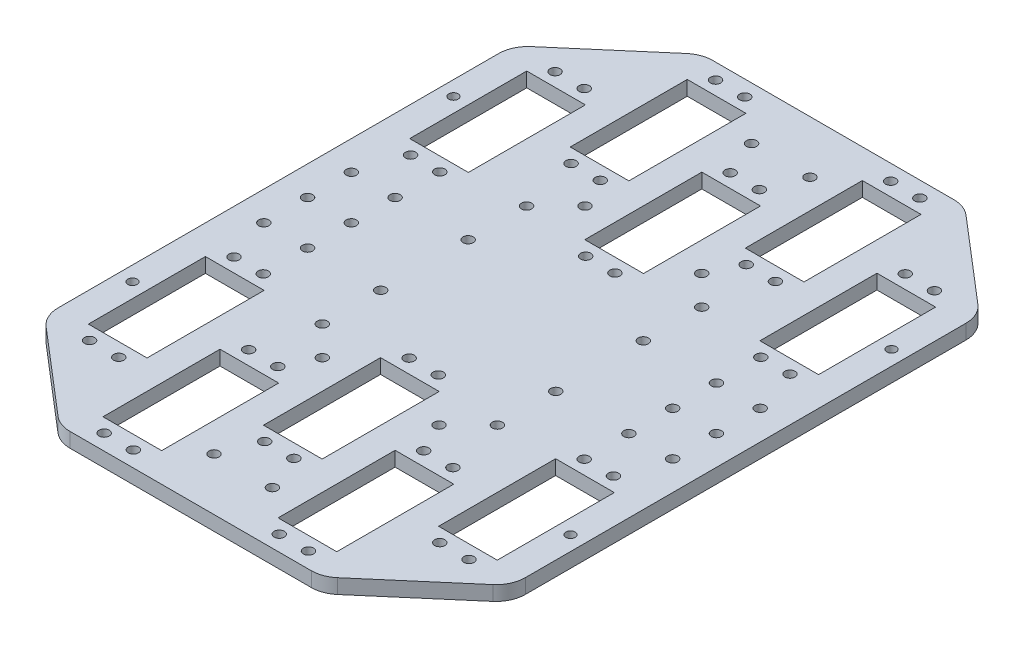
SolidWorks part; units mm, degrees
ref_plane "正面(Front)" through (0, 0, 0) normal (0, 0, 1) x (1, 0, 0)
ref_plane "平面(Top)" through (0, 0, 0) normal (0, 1, 0) x (1, 0, 0)
ref_plane "右側面(Right)" through (0, 0, 0) normal (1, 0, 0) x (0, 0, -1)
sketch "ｽｹｯﾁ1" plane through (0, 0, 0) normal (0, 1, 0) x (1, 0, 0)
  line L0 (0, 0) -> (0, 109.1944) construction
  line L1 (-80.05, 0) -> (80.05, 0)
  line L2 (80.05, 0) -> (80.05, 85.1)
  line L3 (80.05, 85.1) -> (-80.05, 85.1)
  line L4 (-10.05, 20) -> (10.05, 20) construction
  line L5 (-10.05, 50.1) -> (10.05, 50.1)
  line L6 (-10.05, 50.1) -> (-10.05, 10)
  line L7 (-10.05, 10) -> (10.05, 10)
  line L8 (10.05, 50.1) -> (10.05, 10)
  line L9 (-10.05, 50.1) -> (10.05, 10) construction
  line L10 (-10.05, 10) -> (10.05, 50.1) construction
  line L11 (49.95, 50.1) -> (70.05, 50.1)
  line L12 (49.95, 50.1) -> (49.95, 10)
  line L13 (49.95, 10) -> (70.05, 10)
  line L14 (70.05, 50.1) -> (70.05, 10)
  line L15 (49.95, 50.1) -> (70.05, 10) construction
  line L16 (49.95, 10) -> (70.05, 50.1) construction
  line L17 (19.95, 75.1) -> (40.05, 75.1)
  line L18 (19.95, 75.1) -> (19.95, 35)
  line L19 (19.95, 35) -> (40.05, 35)
  line L20 (40.05, 75.1) -> (40.05, 35)
  line L21 (19.95, 75.1) -> (40.05, 35) construction
  line L22 (19.95, 35) -> (40.05, 75.1) construction
  line L23 (19.95, 65.1) -> (40.05, 65.1) construction
  line L24 (-80.05, 0) -> (-80.05, 85.1)
  line L25 (-49.95, 10) -> (-70.05, 10)
  line L26 (-70.05, 50.1) -> (-70.05, 10)
  line L27 (-49.95, 50.1) -> (-70.05, 50.1)
  line L28 (-49.95, 50.1) -> (-49.95, 10)
  line L29 (-19.95, 35) -> (-40.05, 35)
  line L30 (-40.05, 75.1) -> (-40.05, 35)
  line L31 (-19.95, 75.1) -> (-40.05, 75.1)
  line L32 (-19.95, 75.1) -> (-19.95, 35)
  point P3 (60, 30.05)
  point P7 (0, 30.05)
  point P17 (30, 55.05)
  point P26 (0, 85.1)
  dimension "D1" = 10
  dimension "D2" = 10
  dimension "D3" = 40.1
  dimension "D4" = 20.1
  dimension "D5" = 10
  dimension "D6" = 60
  dimension "D7" = 10
  dimension "D8" = 35
  dimension "D9" = 30
  dimension "D10" = 10
  dimension "D11" = 54.1665
extrude "ﾎﾞｽ - 押し出し1" add sketch "ｽｹｯﾁ1" along normal blind 5
sketch "ｽｹｯﾁ2" plane through (0, 5, 0) normal (0, 1, 0) x (1, 0, 0)
  line L0 (0, 0) -> (0, 107.4363) construction
  line L1 (80.05, 55.1) -> (45.05, 85.1)
  line L2 (80.05, 0) -> (80.05, 85.1) construction
  line L3 (80.05, 85.1) -> (-80.05, 85.1) construction
  line L4 (70.05, 50.1) -> (49.95, 50.1) construction
  line L7 (40.05, 35) -> (40.05, 75.1) construction
  line L8 (-80.05, 55.1) -> (-45.05, 85.1)
  line L9 (-45.05, 85.1) -> (45.05, 85.1)
  dimension "D1" = 5
  dimension "D2" = 5
extrude "ｶｯﾄ - 押し出し1" cut sketch "ｽｹｯﾁ2" against normal through all and the other way through all
sketch "ｽｹｯﾁ3" plane through (0, 5, 0) normal (0, 1, 0) x (1, 0, 0)
  line L1 (80.05, 5.25) -> (-114.5257, 5.25) construction
  line L2 (80.05, 0) -> (80.05, 55.1) construction
  line L3 (49.95, 10) -> (70.05, 10) construction
  line L4 (60, 10) -> (60, -5.8436) construction
  line L5 (0, 10) -> (0, -14.4968) construction
  line L6 (-10.05, 10) -> (10.05, 10) construction
  line L7 (-60, 10) -> (-60, -11.451) construction
  line L8 (-70.05, 10) -> (-49.95, 10) construction
  line L9 (-51.2917, 79.75) -> (55, 79.75) construction
  line L10 (-45.05, 85.1) -> (-80.05, 55.1) construction
  line L12 (-19.95, 75.1) -> (-40.05, 75.1) construction
  line L13 (-30, 75.1) -> (-30, 103.3573) construction
  line L14 (30, 75.1) -> (30, 100.8275) construction
  line L15 (40.05, 75.1) -> (19.95, 75.1) construction
  line L16 (81.9855, 54.75) -> (-83.6019, 54.75) construction
  line L17 (70.05, 50.1) -> (49.95, 50.1) construction
  line L18 (60, 50.1) -> (60, 65.5905) construction
  line L19 (0, 50.1) -> (0, 65.5905) construction
  line L20 (10.05, 50.1) -> (-10.05, 50.1) construction
  line L21 (-60, 50.1) -> (-60, 65.5905) construction
  line L22 (-49.95, 50.1) -> (-70.05, 50.1) construction
  line L23 (-55, 30.25) -> (61.2022, 30.25) construction
  line L24 (-40.05, 35) -> (-19.95, 35) construction
  line L25 (-30, 35) -> (-30, 33.4215) construction
  line L26 (30, 35) -> (30, 28.9495) construction
  line L27 (19.95, 35) -> (40.05, 35) construction
  circle A0 centre (65, 5.25) radius 1.75
  circle A1 centre (55, 5.25) radius 1.75
  circle A2 centre (5, 5.25) radius 1.75
  circle A3 centre (-5, 5.25) radius 1.75
  circle A4 centre (-55, 5.25) radius 1.75
  circle A5 centre (-65, 5.25) radius 1.75
  circle A6 centre (-35, 79.75) radius 1.75
  circle A7 centre (-25, 79.75) radius 1.75
  circle A8 centre (25, 79.75) radius 1.75
  circle A9 centre (35, 79.75) radius 1.75
  circle A10 centre (65, 54.75) radius 1.75
  circle A11 centre (55, 54.75) radius 1.75
  circle A12 centre (5, 54.75) radius 1.75
  circle A13 centre (-5, 54.75) radius 1.75
  circle A14 centre (-55, 54.75) radius 1.75
  circle A15 centre (-65, 54.75) radius 1.75
  circle A16 centre (-35, 30.25) radius 1.75
  circle A17 centre (-25, 30.25) radius 1.75
  circle A18 centre (25, 30.25) radius 1.75
  circle A19 centre (35, 30.25) radius 1.75
  dimension "D1" = 4.75
  dimension "D2" = 10
  dimension "D3" = 3.5
  dimension "D4" = 10
  dimension "D5" = 10
  dimension "D7" = 10
  dimension "D8" = 10
  dimension "D10" = 10
  dimension "D11" = 10
  dimension "D12" = 10
  dimension "D14" = 10
  dimension "D15" = 10
  dimension "D6" = 4.65
  dimension "D9" = 4.65
  dimension "D13" = 4.75
extrude "ｶｯﾄ - 押し出し2" cut sketch "ｽｹｯﾁ3" against normal through all
sketch "ｽｹｯﾁ4" plane through (0, 5, 0) normal (0, 1, 0) x (1, 0, 0)
  line L0 (0, 0) -> (0, 98.9038) construction
  line L1 (-80.05, 0) -> (80.05, 0) construction
  circle A0 centre (30, 10) radius 1.75
  circle A1 centre (-30, 10) radius 1.75
  circle A2 centre (20, 20) radius 1.75
  circle A3 centre (-20, 20) radius 1.75
  dimension "D1" = 10
  dimension "D2" = 60
  dimension "D3" = 3.5
  dimension "D4" = 10
  dimension "D5" = 10
extrude "ｶｯﾄ - 押し出し3" cut sketch "ｽｹｯﾁ4" against normal through all
ref_plane "平面1" through (0, 0, 25) normal (0, 0, 1) x (1, 0, 0)
sketch "ｽｹｯﾁ5" plane through (0, 5, 0) normal (0, 1, 0) x (1, 0, 0)
  line L0 (0, 0) -> (0, 107.3691) construction
  line L1 (45.05, 85.1) -> (-45.05, 85.1) construction
  circle A0 centre (-10, 67.1) radius 1.75
  circle A1 centre (10, 67.1) radius 1.75
  dimension "D1" = 3.5
  dimension "D2" = 20
  dimension "D3" = 18
extrude "ｶｯﾄ - 押し出し4" cut sketch "ｽｹｯﾁ5" against normal through all
mirror "ﾐﾗｰ2" about plane through (0, 0, 25) normal (0, 0, 1) of bodies 107 105
sketch "ｽｹｯﾁ6" plane through (0, 5, 0) normal (0, 1, 0) x (1, 0, 0)
  line L0 (-80.05, 0) -> (-80.05, -50)
  line L1 (-80.05, -50) -> (80.05, -50)
  line L2 (80.05, -50) -> (80.05, 0)
  line L3 (80.05, 0) -> (-80.05, 0)
extrude "ﾎﾞｽ - 押し出し2" add sketch "ｽｹｯﾁ6" against normal up to surface (5 mm away) up to face at (-10, 0, -65.35)
sketch "ｽｹｯﾁ7" plane through (0, 5, 0) normal (0, 1, 0) x (1, 0, 0)
  line L0 (-80.05, -25) -> (80.05, -25) construction
  line L1 (-80.05, -105.1) -> (-80.05, 55.1) construction
  line L2 (80.05, 55.1) -> (80.05, -105.1) construction
  line L4 (-30, -10) -> (30, -10) construction
  line L5 (-30, -10) -> (-30, -40) construction
  line L6 (-30, -40) -> (30, -40) construction
  line L7 (30, -10) -> (30, -40) construction
  line L8 (-30, -10) -> (30, -40) construction
  line L9 (-30, -40) -> (30, -10) construction
  circle A0 centre (-30, -10) radius 1.75
  circle A1 centre (-30, -40) radius 1.75
  circle A2 centre (30, -40) radius 1.75
  circle A3 centre (30, -10) radius 1.75
  point P6 (0, -25)
  dimension "D3" = 3.5
  dimension "D1" = 30
  dimension "D2" = 60
extrude "ｶｯﾄ - 押し出し5" cut sketch "ｽｹｯﾁ7" against normal through all
sketch "ｽｹｯﾁ8" plane through (0, 5, 0) normal (0, 1, 0) x (1, 0, 0)
  line L0 (-80.05, -25) -> (80.05, -25) construction
  line L1 (-80.05, -105.1) -> (-80.05, 55.1) construction
  line L2 (80.05, 55.1) -> (80.05, -105.1) construction
  line L3 (0, -25) -> (0, 150.0008) construction
  line L4 (-62.55, -25) -> (-62.55, -69.5543) construction
  circle A0 centre (-70.05, -25) radius 1.75
  circle A1 centre (-70.05, -40) radius 1.75
  circle A2 centre (-70.05, -10) radius 1.75
  circle A3 centre (70.05, -40) radius 1.75
  circle A4 centre (70.05, -25) radius 1.75
  circle A5 centre (70.05, -10) radius 1.75
  circle A6 centre (-75.05, -80) radius 1.6
  circle A7 centre (-75.05, 30) radius 1.6
  circle A8 centre (75.05, -80) radius 1.6
  circle A9 centre (75.05, 30) radius 1.6
  circle A10 centre (-55.05, -10) radius 1.75
  circle A11 centre (-55.05, -25) radius 1.75
  circle A12 centre (-55.05, -40) radius 1.75
  circle A13 centre (55.05, -10) radius 1.75
  circle A14 centre (55.05, -25) radius 1.75
  circle A15 centre (55.05, -40) radius 1.75
  dimension "D1" = 3.5
  dimension "D2" = 10
  dimension "D3" = 15
  dimension "D4" = 5
  dimension "D5" = 3.2
  dimension "D6" = 55
  dimension "D7" = 7.5
extrude "ｶｯﾄ - 押し出し6" cut sketch "ｽｹｯﾁ8" against normal through all
fillet "ﾌｨﾚｯﾄ1" radius 10 8 edges at (-80.05, 2.5, -55.1) (-45.05, 2.5, -85.1) (45.05, 2.5, -85.1) (80.05, 2.5, -55.1) (45.05, 2.5, 135.1) (80.05, 2.5, 105.1) (-45.05, 2.5, 135.1) (-80.05, 2.5, 105.1)
